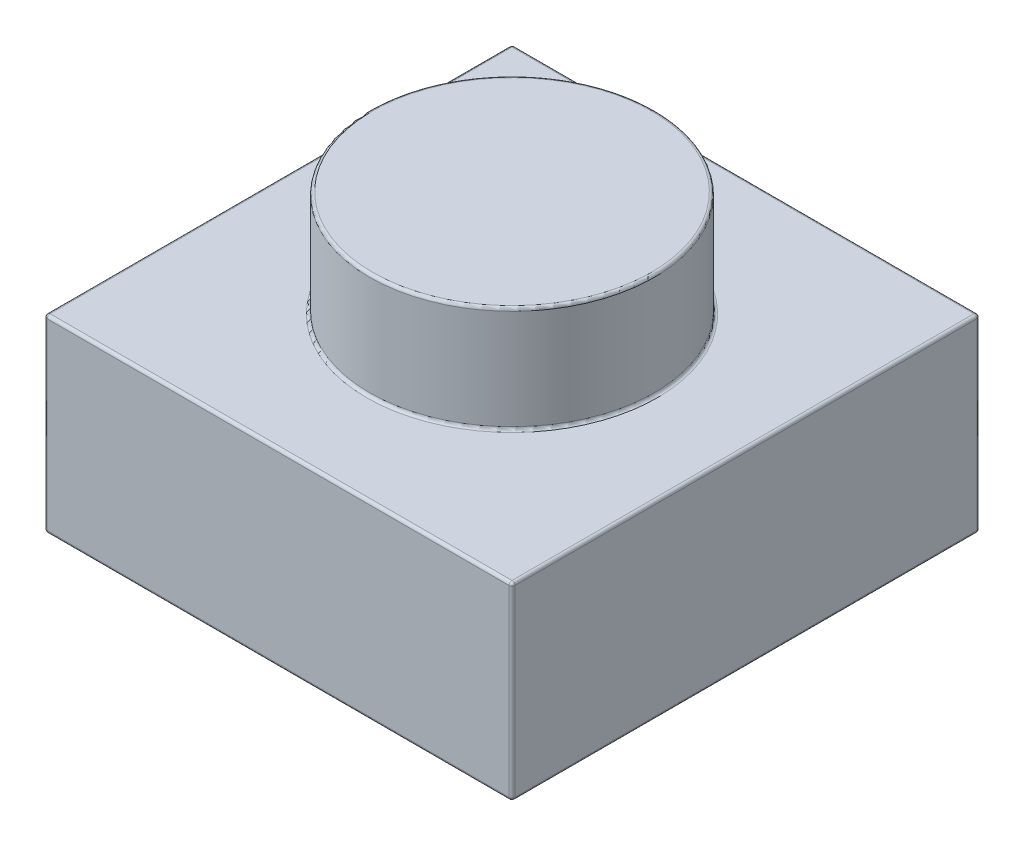
SolidWorks part; units mm, degrees
material "Red Clear Plastic"
ref_plane "Front Plane" through (0, 0, 0) normal (0, 0, 1) x (1, 0, 0)
ref_plane "Top Plane" through (0, 0, 0) normal (0, 1, 0) x (1, 0, 0)
ref_plane "Right Plane" through (0, 0, 0) normal (1, 0, 0) x (0, 0, -1)
sketch "Sketch1" plane through (0, 0, 0) normal (0, 1, 0) x (1, 0, 0)
  line L1 (-3.98, 3.98) -> (3.98, 3.98)
  line L2 (-3.98, 3.98) -> (-3.98, -3.98)
  line L3 (-3.98, -3.98) -> (3.98, -3.98)
  line L4 (3.98, 3.98) -> (3.98, -3.98)
  line L5 (-3.98, 3.98) -> (3.98, -3.98) construction
  line L6 (-3.98, -3.98) -> (3.98, 3.98) construction
  point P0 (0, 0)
  dimension "D1" = 7.96
extrude "Extrude1" add sketch "Sketch1" along normal blind 3.22
sketch "Sketch2" plane through (0, 3.22, 0) normal (0, 1, 0) x (1, 0, 0)
  circle A0 centre (0, 0) radius 2.425
  dimension "D1" = 4.85
extrude "Extrude2" add sketch "Sketch2" along normal blind 1.8
shell "Shell1" thickness 1.55
sketch "Sketch3" plane through (0, 1.67, 0) normal (0, -1, 0) x (1, 0, 0)
  line L0 (2.43, -2.43) -> (-2.43, -2.43) construction
  line L1 (-2.43, -2.43) -> (-2.43, 2.43) construction
  line L2 (-2.43, 2.43) -> (2.43, 2.43) construction
  line L3 (2.43, 2.43) -> (2.43, -2.43) construction
  line L4 (2.43, -2.43) -> (-2.43, -2.43)
  line L5 (-2.43, -2.43) -> (-2.43, 2.43)
  line L6 (-2.43, 2.43) -> (2.43, 2.43)
  line L7 (2.43, 2.43) -> (2.43, -2.43)
extrude "Extrude3" cut sketch "Sketch3" against normal blind 0.14
fillet "Fillet1" radius 0.05 28 edges at (2.43, 1.81, 0) (0, 1.81, 2.43) (-2.43, 1.81, 0) (0, 1.81, -2.43) (0, 1.81, 0.875) (0, 3.47, 0.875) (2.43, 0, 0) (0, 0, -2.43) (-2.43, 0, 0) (0, 0, 2.43) (2.43, 0.905, 2.43) (-2.43, 0.905, 2.43) (-2.43, 0.905, -2.43) (2.43, 0.905, -2.43) (0, 3.22, 2.425) (0, 5.02, 2.425) (3.98, 0, 0) (0, 0, -3.98) (-3.98, 0, 0) (0, 0, 3.98) (3.98, 3.22, 0) (0, 3.22, -3.98) (-3.98, 3.22, 0) (0, 3.22, 3.98) (3.98, 1.61, 3.98) (-3.98, 1.61, 3.98) (-3.98, 1.61, -3.98) (3.98, 1.61, -3.98)
